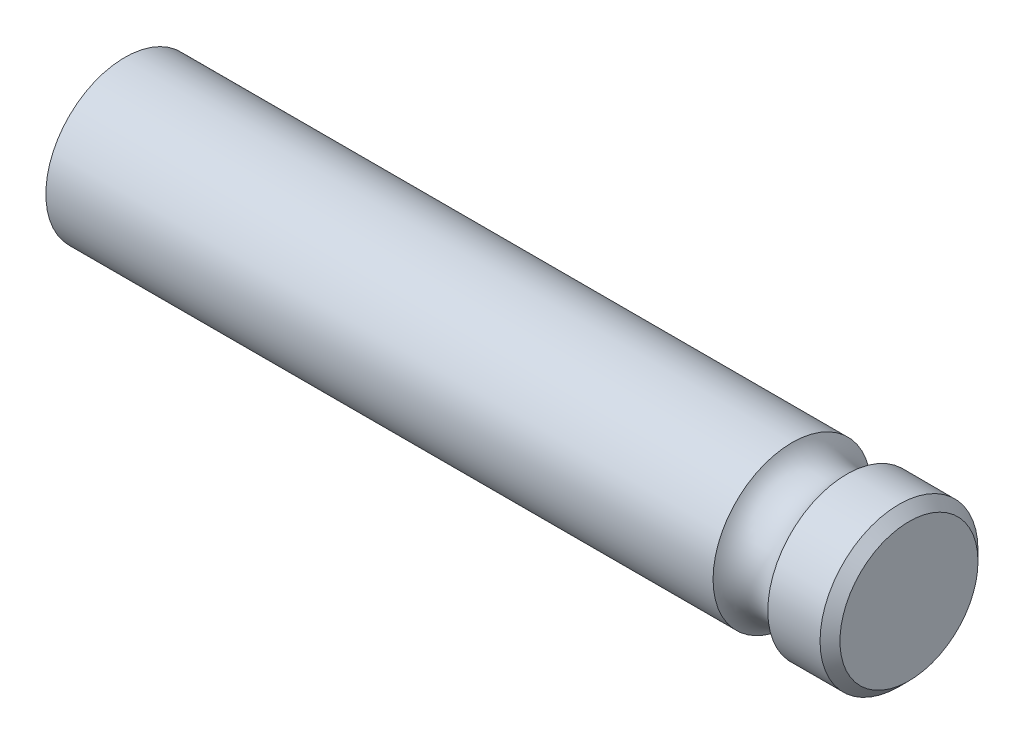
SolidWorks part; units mm, degrees
material "Plain Carbon Steel"
ref_plane "Front Plane" through (0, 0, 0) normal (0, 0, 1) x (1, 0, 0)
ref_plane "Top Plane" through (0, 0, 0) normal (0, 1, 0) x (1, 0, 0)
ref_plane "Right Plane" through (0, 0, 0) normal (1, 0, 0) x (0, 0, -1)
sketch "Sketch1" plane through (0, 0, 0) normal (1, 0, 0) x (0, 0, -1)
  circle A0 centre (0, 0) radius 7.9375
  dimension "D1" = 15.875
extrude "Extrude1" add sketch "Sketch1" along normal blind 78.8
sketch "Sketch2" plane through (0, 0, 0) normal (0, 1, 0) x (1, 0, 0)
  line L0 (78.8, -7.9375) -> (78.8, 7.9375) construction
  line L1 (0, 0) -> (88.2059, 0) construction
  line L2 (69.8, 6.35) -> (83.0563, 6.35) construction
  circle A0 centre (69.8, 9.525) radius 3.175
  dimension "D1" = 9
  dimension "D2" = 6.35
  dimension "D3" = 6.35
revolve "Cut-Revolve1" cut sketch "Sketch2" angle 360 about L1
chamfer "Chamfer1" distance 1 angle 45 1 edges at (78.8, 0, -7.9375)
sketch3d "3DSketch1"
  line L0 (0, 0, 0) -> (78.8, 0, 0) construction
  line L1 (77.8, 0, 0) -> (78.8, 0, 0) construction
  line L2 (78.8, 0, 0) -> (149.792, 0, 0) construction
  line L3 (0, 0, 0) -> (-93.4801, 0, 0) construction
